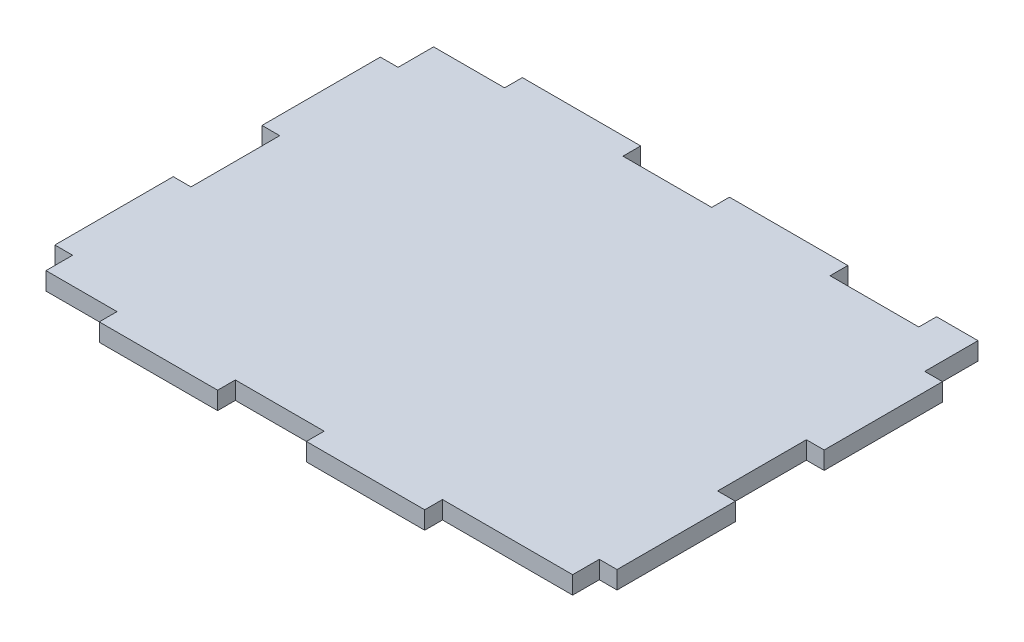
SolidWorks part; units mm, degrees
ref_plane "Front Plane" through (0, 0, 0) normal (0, 0, 1) x (1, 0, 0)
ref_plane "Top Plane" through (0, 0, 0) normal (0, 1, 0) x (1, 0, 0)
ref_plane "Right Plane" through (0, 0, 0) normal (1, 0, 0) x (0, 0, -1)
sketch "Sketch1" plane through (0, 0, 0) normal (0, 1, 0) x (1, 0, 0)
  line L0 (12, 65.5) -> (0, 65.5)
  line L1 (89, 0) -> (67, 0)
  line L2 (89, 0) -> (89, 4.5)
  line L3 (82, 65.5) -> (67, 65.5)
  line L4 (0, 0) -> (0, 4.5)
  line L5 (47, 65.5) -> (32, 65.5)
  line L6 (12, 65.5) -> (12, 68.5)
  line L7 (12, 68.5) -> (32, 68.5)
  line L8 (32, 65.5) -> (32, 68.5)
  line L11 (89, 59.5) -> (89, 65.5)
  line L12 (47, 65.5) -> (47, 68.5)
  line L13 (47, 68.5) -> (67, 68.5)
  line L14 (67, 65.5) -> (67, 68.5)
  line L15 (89, 65.5) -> (89, 68.5)
  line L16 (89, 68.5) -> (82, 68.5)
  line L17 (0, 59.5) -> (-3, 59.5)
  line L18 (82, 65.5) -> (82, 68.5)
  line L19 (0, 24.5) -> (-3, 24.5)
  line L20 (-3, 59.5) -> (-3, 39.5)
  line L23 (0, 39.5) -> (-3, 39.5)
  line L24 (0, 59.5) -> (0, 65.5)
  line L25 (0, 4.5) -> (-3, 4.5)
  line L26 (-3, 24.5) -> (-3, 4.5)
  line L29 (0, 39.5) -> (0, 24.5)
  line L30 (12, 0) -> (12, -3)
  line L31 (12, -3) -> (32, -3)
  line L32 (32, 0) -> (32, -3)
  line L35 (12, 0) -> (0, 0)
  line L36 (47, 0) -> (47, -3)
  line L37 (47, -3) -> (67, -3)
  line L38 (67, 0) -> (67, -3)
  line L41 (89, 4.5) -> (92, 4.5)
  line L42 (47, 0) -> (32, 0)
  line L43 (89, 39.5) -> (92, 39.5)
  line L44 (92, 4.5) -> (92, 24.5)
  line L47 (89, 59.5) -> (92, 59.5)
  line L48 (89, 39.5) -> (89, 24.5)
  line L49 (89, 24.5) -> (92, 24.5)
  line L50 (92, 59.5) -> (92, 39.5)
  point P24 (0, 0)
  point P29 (0, 0)
  point P34 (0, 0)
  dimension "D1" = 20
  dimension "D2" = 89
  dimension "D3" = 65.5
  dimension "D4" = 3
  dimension "D5" = 6
  dimension "D6" = 15
  dimension "D7" = 12
  dimension "D8" = 7
extrude "Boss-Extrude1" add sketch "Sketch1" along normal blind 3
